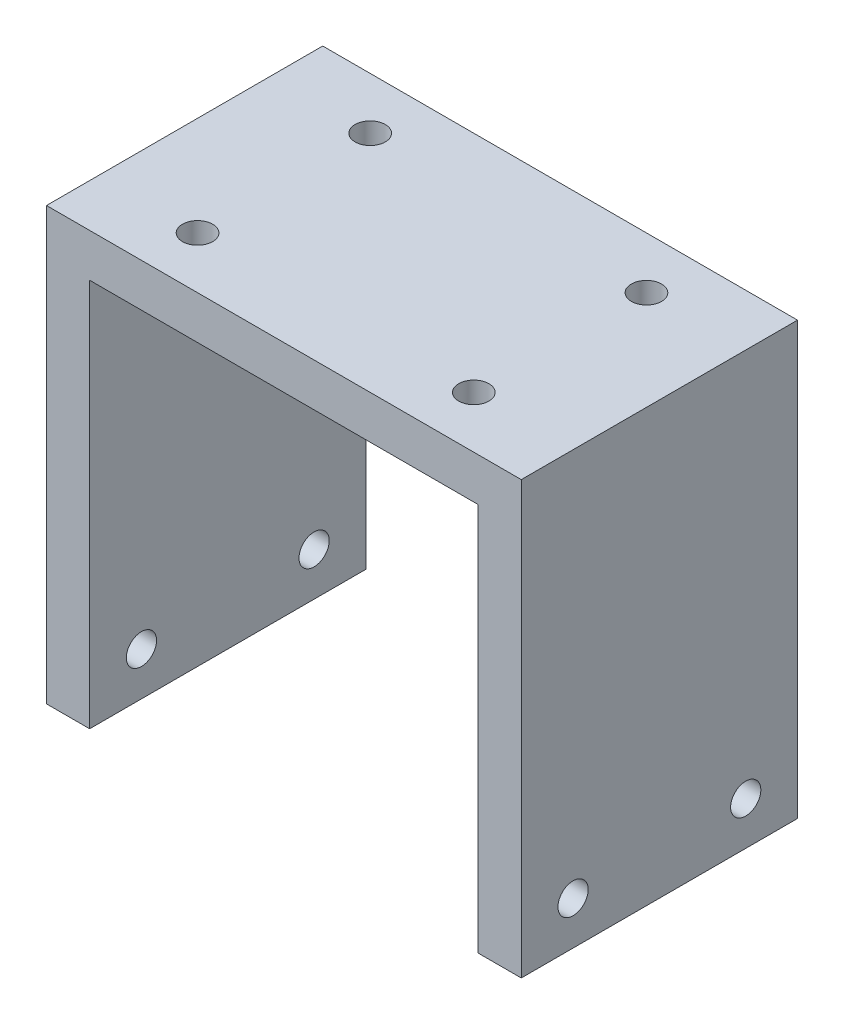
SolidWorks part; units mm, degrees
ref_plane "Front Plane" through (0, 0, 0) normal (0, 0, 1) x (1, 0, 0)
ref_plane "Top Plane" through (0, 0, 0) normal (0, 1, 0) x (1, 0, 0)
ref_plane "Right Plane" through (0, 0, 0) normal (1, 0, 0) x (0, 0, -1)
sketch "Sketch1" plane through (0, 0, 0) normal (0, 1, 0) x (1, 0, 0)
  line L1 (0, 0) -> (55, 0)
  line L2 (0, 0) -> (0, 32)
  line L3 (0, 32) -> (55, 32)
  line L4 (55, 0) -> (55, 32)
  dimension "D1" = 32
  dimension "D2" = 55
extrude "Boss-Extrude1" add sketch "Sketch1" along normal blind 50
sketch "Sketch2" plane through (0, 0, 0) normal (0, -1, 0) x (1, 0, 0)
  line L0 (0, 0) -> (55, 0) construction
  line L1 (5, 0) -> (50, 0)
  line L2 (5, 0) -> (5, -32)
  line L3 (5, -32) -> (50, -32)
  line L4 (50, 0) -> (50, -32)
  line L5 (55, -32) -> (0, -32) construction
  line L6 (0, -32) -> (0, 0) construction
  line L7 (55, 0) -> (55, -32) construction
  dimension "D1" = 5
  dimension "D2" = 5
extrude "Cut-Extrude1" cut sketch "Sketch2" against normal blind 45
sketch "Sketch3" plane through (0, 50, 0) normal (0, 1, 0) x (1, 0, 0)
  line L0 (55, 32) -> (0, 32) construction
  line L1 (55, 0) -> (55, 32) construction
  circle A0 centre (43.5, 26) radius 1.75
  circle A1 centre (43.5, 6) radius 1.75
  circle A2 centre (11.5, 26) radius 1.75
  circle A3 centre (11.5, 6) radius 1.75
  point P8 (41.7039, 24.6636)
  point P9 (12.1042, 24.2886)
  dimension "D1" = 3.5
  dimension "D2" = 20
  dimension "D3" = 20
  dimension "D4" = 32
  dimension "D5" = 32
  dimension "D6" = 6
  dimension "D7" = 11.5
extrude "Cut-Extrude2" cut sketch "Sketch3" against normal through all
sketch "Sketch4" plane through (55, 0, 0) normal (1, 0, 0) x (0, 0, -1)
  line L0 (0, 50) -> (32, 50) construction
  line L1 (0, 50) -> (0, 0) construction
  circle A0 centre (6, 5) radius 1.75
  circle A1 centre (26, 5) radius 1.75
  dimension "D1" = 3.5
  dimension "D2" = 3.5
  dimension "D3" = 20
  dimension "D4" = 45
  dimension "D5" = 6
extrude "Cut-Extrude3" cut sketch "Sketch4" against normal through all
sketch "Sketch5" plane through (50, 0, 0) normal (-1, 0, 0) x (0, 0, 1)
  line L0 (-30, 10) -> (-28.9, 10)
  line L1 (-32, 45) -> (-30.9, 45)
  line L2 (-32, 45) -> (-32, 10)
  line L3 (-32, 10) -> (-30.9, 10)
  line L4 (-30.9, 45) -> (-30.9, 10)
  line L5 (-28.9, 45) -> (-28.9, 10)
  line L6 (-30, 45) -> (-30, 10)
  line L7 (-30, 45) -> (-28.9, 45)
  line L8 (-28, 10) -> (-26.9, 10)
  line L9 (-26.9, 45) -> (-26.9, 10)
  line L10 (-28, 45) -> (-28, 10)
  line L11 (-28, 45) -> (-26.9, 45)
  line L12 (-26, 10) -> (-24.9, 10)
  line L13 (-24.9, 45) -> (-24.9, 10)
  line L14 (-26, 45) -> (-26, 10)
  line L15 (-26, 45) -> (-24.9, 45)
  line L16 (-24, 10) -> (-22.9, 10)
  line L17 (-22.9, 45) -> (-22.9, 10)
  line L18 (-24, 45) -> (-24, 10)
  line L19 (-24, 45) -> (-22.9, 45)
  line L20 (-22, 10) -> (-20.9, 10)
  line L21 (-20.9, 45) -> (-20.9, 10)
  line L22 (-22, 45) -> (-22, 10)
  line L23 (-22, 45) -> (-20.9, 45)
  line L24 (-20, 10) -> (-18.9, 10)
  line L25 (-18.9, 45) -> (-18.9, 10)
  line L26 (-20, 45) -> (-20, 10)
  line L27 (-20, 45) -> (-18.9, 45)
  line L28 (-18, 10) -> (-16.9, 10)
  line L29 (-16.9, 45) -> (-16.9, 10)
  line L30 (-18, 45) -> (-18, 10)
  line L31 (-18, 45) -> (-16.9, 45)
  line L32 (-16, 10) -> (-14.9, 10)
  line L33 (-14.9, 45) -> (-14.9, 10)
  line L34 (-16, 45) -> (-16, 10)
  line L35 (-16, 45) -> (-14.9, 45)
  line L36 (-14, 10) -> (-12.9, 10)
  line L37 (-12.9, 45) -> (-12.9, 10)
  line L38 (-14, 45) -> (-14, 10)
  line L39 (-14, 45) -> (-12.9, 45)
  line L40 (-12, 10) -> (-10.9, 10)
  line L41 (-10.9, 45) -> (-10.9, 10)
  line L42 (-12, 45) -> (-12, 10)
  line L43 (-12, 45) -> (-10.9, 45)
  line L44 (-10, 10) -> (-8.9, 10)
  line L45 (-8.9, 45) -> (-8.9, 10)
  line L46 (-10, 45) -> (-10, 10)
  line L47 (-10, 45) -> (-8.9, 45)
  line L48 (-8, 10) -> (-6.9, 10)
  line L49 (-6.9, 45) -> (-6.9, 10)
  line L50 (-8, 45) -> (-8, 10)
  line L51 (-8, 45) -> (-6.9, 45)
  line L52 (-6, 10) -> (-4.9, 10)
  line L53 (-4.9, 45) -> (-4.9, 10)
  line L54 (-6, 45) -> (-6, 10)
  line L55 (-6, 45) -> (-4.9, 45)
  line L56 (-4, 10) -> (-2.9, 10)
  line L57 (-2.9, 45) -> (-2.9, 10)
  line L58 (-4, 45) -> (-4, 10)
  line L59 (-4, 45) -> (-2.9, 45)
  line L60 (-2, 10) -> (-0.9, 10)
  line L61 (-0.9, 45) -> (-0.9, 10)
  line L62 (-2, 45) -> (-2, 10)
  line L63 (-2, 45) -> (-0.9, 45)
  line L64 (0, 10) -> (1.1, 10)
  line L65 (1.1, 45) -> (1.1, 10)
  line L66 (0, 45) -> (0, 10)
  line L67 (0, 45) -> (1.1, 45)
  dimension "D1" = 35
  dimension "D2" = 1.1
  dimension "D3" = 17
extrude "Cut-Extrude4" cut sketch "Sketch5" against normal blind 1.2
